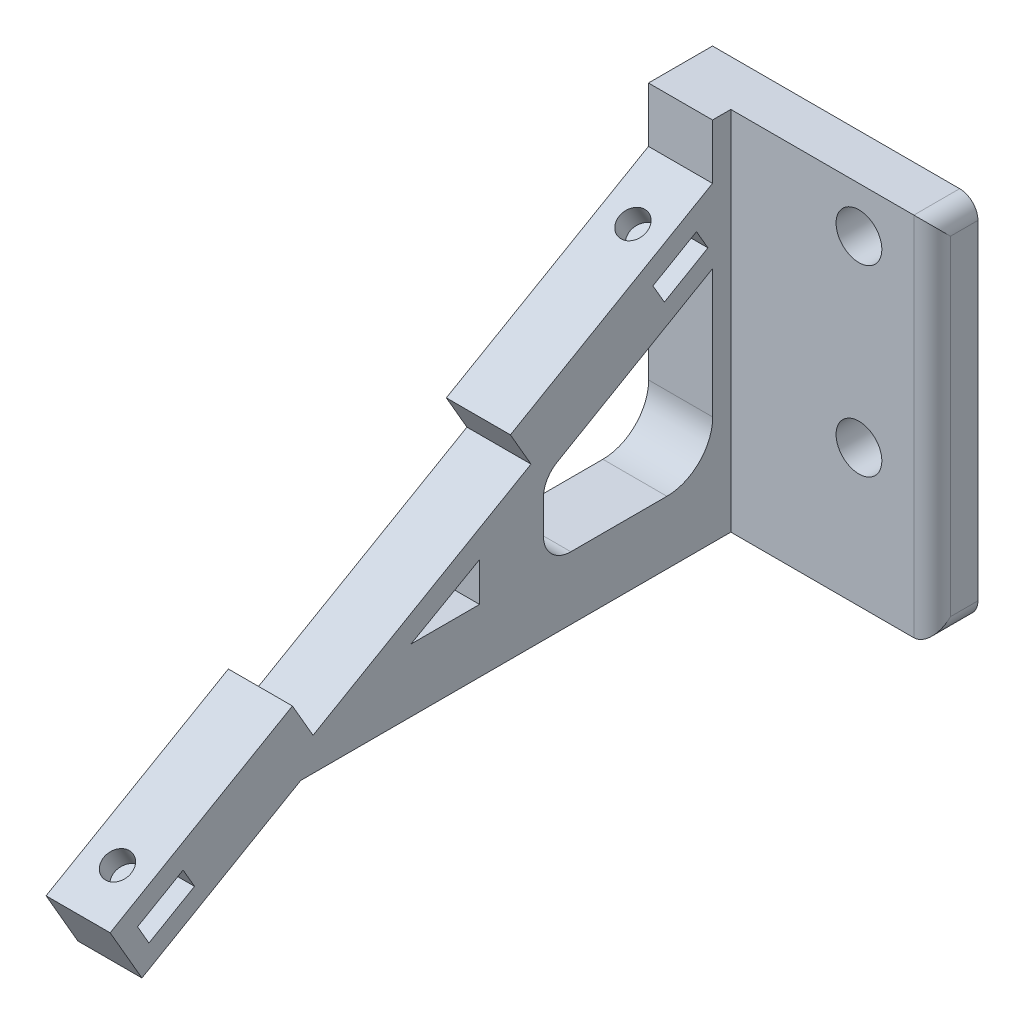
SolidWorks part; units mm, degrees
ref_plane "Front Plane" through (0, 0, 0) normal (0, 0, 1) x (1, 0, 0)
ref_plane "Top Plane" through (0, 0, 0) normal (0, 1, 0) x (1, 0, 0)
ref_plane "Right Plane" through (0, 0, 0) normal (1, 0, 0) x (0, 0, -1)
other "Mesh1"
sketch "Sketch1" plane through (0, 0, 0) normal (1, 0, 0) x (0, 0, -1)
  line L0 (-90932.5796, -4234.1019) -> (-71013.9953, 7265.8981)
  line L1 (-71013.9953, 7265.8981) -> (-68763.9953, 3368.7838)
  line L2 (-68763.9953, 3368.7838) -> (-44948.2967, 17118.7838)
  line L3 (-44948.2967, 17118.7838) -> (-47198.2967, 21015.8981)
  line L4 (-47198.2967, 21015.8981) -> (-25114.6489, 33765.8981)
  line L5 (-25114.6489, 33765.8981) -> (-25114.6489, 39765.8981)
  line L6 (-25114.6489, 39765.8981) -> (-18114.6489, 39765.8981)
  line L7 (-18114.6489, 39765.8981) -> (-18114.6489, -234.1019)
  line L8 (-90932.5796, -4234.1019) -> (-89130.3388, -4234.1019) construction
  line L9 (-18114.6489, -234.1019) -> (-70107.2704, -234.1019)
  line L10 (-70107.2704, -234.1019) -> (-87458.3031, -10251.7253)
  line L11 (-90932.5796, -4234.1019) -> (-87458.3031, -10251.7253)
  line L12 (-87940.7843, -5162.9479) -> (-82961.1382, -2287.9479)
  line L13 (-82961.1382, -2287.9479) -> (-81711.1382, -4453.0115)
  line L14 (-81711.1382, -4453.0115) -> (-86690.7843, -7328.0115)
  line L15 (-86690.7843, -7328.0115) -> (-87940.7843, -5162.9479)
  line L16 (-58064.4113, 6650.0317) -> (-50564.4113, 10900.0317)
  line L17 (-50564.4113, 10900.0317) -> (-50564.4113, 6650.0317)
  line L18 (-50564.4113, 6650.0317) -> (-58064.4113, 6650.0317)
  line L19 (-31627.1311, 27323.1447) -> (-26867.0679, 30078.4664)
  line L20 (-26867.0679, 30078.4664) -> (-25614.6489, 27914.8013)
  line L21 (-25614.6489, 27914.8013) -> (-30374.7122, 25159.4795)
  line L22 (-30374.7122, 25159.4795) -> (-31627.1311, 27323.1447)
  line L23 (-25094.8426, 25713.3197) -> (-25094.8426, 11650.0317)
  line L24 (-30094.8426, 6650.0317) -> (-40594.8426, 6650.0317)
  line L25 (-43594.8426, 13308.0426) -> (-43594.8426, 9650.0317)
  line L26 (-25094.8426, 25713.3197) -> (-42094.8426, 15873.0159)
  arc A0 (-30094.8426, 6650.0317) -> (-25094.8426, 11650.0317) centre (-30094.8426, 11650.0317) ccw
  arc A1 (-43594.8426, 9650.0317) -> (-40594.8426, 6650.0317) centre (-40594.8426, 9650.0317) ccw
  arc A2 (-42094.8426, 15873.0159) -> (-43594.8426, 13271.5835) centre (-40589.0258, 13271.5835) ccw
  point P24 (0, 0)
  point P27 (-89130.3388, -4234.1019)
  point P30 (-25675.9814, 27914.8013)
  dimension "D24" = 5000
  dimension "D28" = 3000
  dimension "D1" = 23000
  dimension "D2" = 4500
  dimension "D3" = 27500
  dimension "D4" = 4500
  dimension "D5" = 30
  dimension "D6" = 6000
  dimension "D7" = 25500
  dimension "D8" = 7000
  dimension "D9" = 40000
  dimension "D10" = 51992.6215
  dimension "D11" = 150
  dimension "D12" = 5500
  dimension "D13" = 2500
  dimension "D14" = 7500
  dimension "D15" = 4250
  dimension "D16" = 5750
  dimension "D17" = 2500
  dimension "D18" = 2148.2511
  dimension "D19" = 2126.5478
  dimension "D20" = 6884.1336
  dimension "D21" = 32868.1683
  dimension "D22" = 11980.1937
  dimension "D23" = 25947.4217
  dimension "D25" = 17000
  dimension "D26" = 9840.3039
  dimension "D27" = 10500
  dimension "D29" = 25393.5815
  dimension "D30" = 7500
extrude "Boss-Extrude1" add sketch "Sketch1" against normal blind 7000
ref_plane "Plane1" through (0, 36285.9881, 20949.725) normal (0, 0.866, 0.5) x (1, 0, 0)
sketch "Sketch2" plane through (0, 0, 0) normal (0, 0, 1) x (1, 0, 0)
  line L0 (-40483.4755, -7522.2196) -> (-47474.8479, -7522.2196)
sketch "Sketch3" plane through (0, 0, 0) normal (0, 0, 1) x (1, 0, 0)
  line L0 (-40477.0787, 39685.295) -> (-69477.0787, 39685.295)
  line L1 (-40477.0787, 39685.295) -> (-40477.0787, -314.705)
  line L2 (-40477.0787, -314.705) -> (-69477.0787, -314.705)
  line L3 (-69477.0787, 39685.295) -> (-69477.0787, -314.705)
  circle A0 centre (-61434.2787, 34700.8694) radius 2612.0723
  circle A1 centre (-61482.2069, 9690.1301) radius 2582.0747
  circle A2 centre (-67486.5197, 37694.736) radius 1990.559
  dimension "D1" = 29000
  dimension "D2" = 40000
  dimension "D3" = 10004.8352
  dimension "D4" = 35015.5744
  dimension "D5" = 7994.8718
sketch "Sketch6" plane through (0, 0, 0) normal (1, 0, 0) x (0, 0, -1)
  line L0 (-18114.6489, 24672.3169) -> (-23139.1932, 24672.3169)
  line L1 (-18114.6489, 39765.8981) -> (-18114.6489, -234.1019) construction
sketch "Sketch8" plane through (0, 0, 18114.6489) normal (0, 0, -1) x (-1, 0, 0)
  line L0 (29000, 39765.8981) -> (0, 39765.8981)
  line L1 (0, 39765.8981) -> (0, -234.1019)
  line L2 (0, -234.1019) -> (29000, -234.1019)
  line L3 (29000, -234.1019) -> (29000, 39765.8981)
  line L4 (21000, 14765.8981) -> (21000, 34765.8981) construction
  line L5 (7000, 39765.8981) -> (0, 39765.8981) construction
  circle A0 centre (21000, 14765.8981) radius 2500
  circle A1 centre (21000, 34765.8981) radius 2500
  point P8 (0, 0)
  point P10 (0, 39765.8981)
  dimension "D5" = 5000
  dimension "D1" = 29000
  dimension "D2" = 15000
  dimension "D3" = 35000
  dimension "D4" = 8000
extrude "Boss-Extrude3" add sketch "Sketch8" against normal blind 5000
fillet "Fillet1" radius 2000 3 edges at (-29000, -234.1019, 20614.6489) (-29000, 39765.8981, 20614.6489) (-29000, 19765.8981, 23114.6489)
sketch "Sketch9" plane through (0, 36199.3855, 20899.725) normal (0, 0.866, 0.5) x (1, 0, 0)
  line L0 (-44195.3034, -10868.8212) -> (-3500, -10868.8212) construction
  line L1 (-44228.7555, -75902.8757) -> (-3500, -75902.8757) construction
  line L2 (-40674.3613, -12602.0022) -> (-40674.3613, -7750.6514) construction
  line L3 (0, -30366.9749) -> (0, -4866.9749) construction
  line L4 (-3500, -10868.8212) -> (-3500, -75902.8757) construction
  circle A1 centre (-44228.7555, -75902.8757) radius 1517.8112 construction
  circle A2 centre (-44195.3034, -10868.8212) radius 1458.892 construction
  circle A3 centre (-3500, -10868.8212) radius 1500
  circle A4 centre (-3500, -75902.8757) radius 1500
  dimension "D1" = 2917.784
  dimension "D3" = 3000
  dimension "D4" = 3000
  dimension "D2" = 3520.9421
  dimension "D5" = 3500
extrude "Cut-Extrude1" cut sketch "Sketch9" against normal blind 7500
mirror "Mirror1" about plane through (0, 0, 0) normal (1, 0, 0) of "Cut-Extrude1", "Fillet1", "Boss-Extrude3", "Boss-Extrude1"
sketch "Sketch10" plane through (0, 0, 18114.6489) normal (0, 0, -1) x (-1, 0, 0)
  line L1 (0, -10251.7253) -> (30032.7485, -10251.7253)
  line L2 (0, -10251.7253) -> (0, 39765.8981)
  line L3 (0, 39765.8981) -> (30032.7485, 39765.8981)
  line L4 (30032.7485, -10251.7253) -> (30032.7485, 39765.8981)
  line L5 (7000, -10251.7253) -> (-7000, -10251.7253) construction
  line L6 (27000, 39765.8981) -> (-27000, 39765.8981) construction
  line L7 (36208.2248, 35016.3215) -> (34433.6516, 35016.3215)
  line L8 (36208.2248, 35016.3215) -> (36208.2248, 39958.7206)
  line L9 (36208.2248, 39958.7206) -> (34433.6516, 39958.7206)
  line L10 (34433.6516, 35016.3215) -> (34433.6516, 39958.7206)
  point P4 (0, -10251.7253)
  point P6 (30032.7485, 0)
  point P12 (0, 39765.8981)
extrude "Cut-Extrude2" cut sketch "Sketch10" against normal through all
